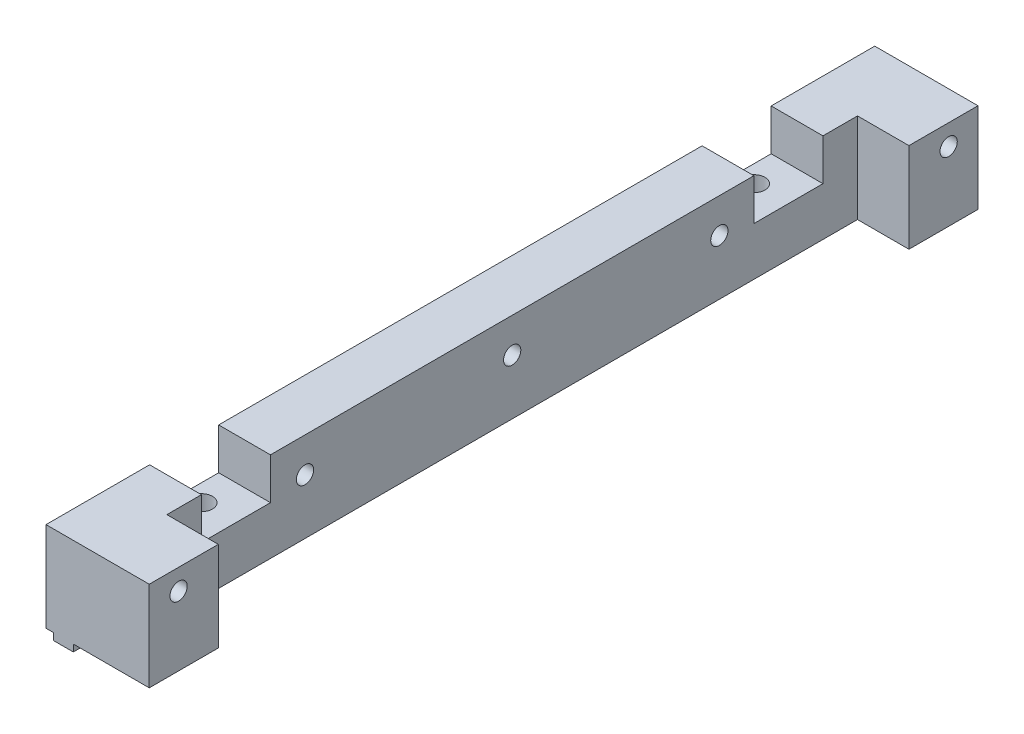
SolidWorks part; units mm, degrees
ref_plane "Front Plane" through (0, 0, 0) normal (0, 0, 1) x (1, 0, 0)
ref_plane "Top Plane" through (0, 0, 0) normal (0, 1, 0) x (1, 0, 0)
ref_plane "Right Plane" through (0, 0, 0) normal (1, 0, 0) x (0, 0, -1)
sketch "Esquisse1" plane through (0, 0, 0) normal (0, 0, 1) x (1, 0, 0)
  line L0 (0, 13) -> (14.95, 13)
  line L1 (14.95, 13) -> (14.95, 0)
  line L2 (14.95, 0) -> (3.95, 0)
  line L3 (3.95, 0) -> (3.95, -1)
  line L4 (3.95, -1) -> (1.05, -1)
  line L5 (1.05, -1) -> (1.05, 0)
  line L6 (1.05, 0) -> (0, 0)
  line L7 (0, 0) -> (0, 13)
  dimension "D1" = 11
  dimension "D2" = 13
  dimension "D3" = 1
  dimension "D4" = 2.9
  dimension "D5" = 1.05
  dimension "D6" = 14.95
extrude "Main" add sketch "Esquisse1" along normal mid plane 120
sketch "Esquisse2" plane through (14.95, 0, 0) normal (1, 0, 0) x (0, 0, -1)
  line L0 (-60, 0) -> (60, 0) construction
  line L1 (-55.75, 10) -> (55.75, 10) construction
  line L3 (-60, 13) -> (60, 13) construction
  circle A0 centre (55.75, 10) radius 1.25
  circle A1 centre (-55.75, 10) radius 1.25
  point P8 (0, 13)
  point P9 (0, 10)
  dimension "D1" = 111.5
  dimension "D3" = 2.5
  dimension "D2" = 10
extrude "HolesForMotorBoard" cut sketch "Esquisse2" against normal through all
sketch "Esquisse4" plane through (0, -1, 0) normal (0, -1, 0) x (-1, 0, 0)
  line L0 (0, -60) -> (0, 60) construction
  line L1 (-1.05, -60) -> (-3.95, -60) construction
  line L2 (-1.05, 60) -> (-3.95, 60) construction
  circle A0 centre (-2.5, -40) radius 1.6
  circle A1 centre (-2.5, 40) radius 1.6
  dimension "D1" = 3.2
  dimension "D2" = 2.5
  dimension "D3" = 20
  dimension "D4" = 20
extrude "HolesForMakerBeam" cut sketch "Esquisse4" against normal through all
sketch "Sketch1" plane through (14.95, 0, 0) normal (1, 0, 0) x (0, 0, -1)
  line L0 (-60, 13) -> (60, 13) construction
  line L1 (50, 0) -> (-50, 0)
  line L2 (50, 0) -> (50, 13)
  line L3 (50, 13) -> (-50, 13)
  line L4 (-50, 0) -> (-50, 13)
  line L5 (60, 0) -> (60, 13) construction
  line L6 (-60, 0) -> (-60, 13) construction
  line L7 (-60, 0) -> (60, 0) construction
  point P8 (60, 6.5)
  dimension "D1" = 10
  dimension "D2" = 10
extrude "PowerBoardPinHoles" cut sketch "Sketch1" against normal blind 7.45
sketch "Sketch2" plane through (0, 0, 0) normal (-1, 0, 0) x (0, 0, 1)
  line L0 (60, 13) -> (-60, 13) construction
  circle A0 centre (0, 8) radius 1.25
  circle A1 centre (-30, 8) radius 1.25
  circle A2 centre (30, 8) radius 1.25
  point P3 (0, 13)
  dimension "D1" = 2.5
  dimension "D2" = 5
  dimension "D3" = 30
  dimension "D4" = 30
extrude "WindowFixHoles" cut sketch "Sketch2" against normal through all
sketch "Sketch3" plane through (0, 0, 0) normal (-1, 0, 0) x (0, 0, 1)
  line L0 (60, 13) -> (-60, 13) construction
  line L1 (-35, 13) -> (-45, 13)
  line L2 (-35, 13) -> (-35, 7)
  line L3 (-35, 7) -> (-45, 7)
  line L4 (-45, 13) -> (-45, 7)
  line L5 (60, 0) -> (-60, 0) construction
  line L6 (35, 7) -> (45, 7)
  line L7 (35, 7) -> (35, 13)
  line L8 (35, 13) -> (45, 13)
  line L9 (45, 7) -> (45, 13)
  point P12 (-51.301, 6.5)
  point P13 (35.0226, 7)
  dimension "D1" = 7
  dimension "D2" = 10
  dimension "D3" = 35
  dimension "D4" = 35
extrude "Cut-Extrude1" cut sketch "Sketch3" against normal through all
